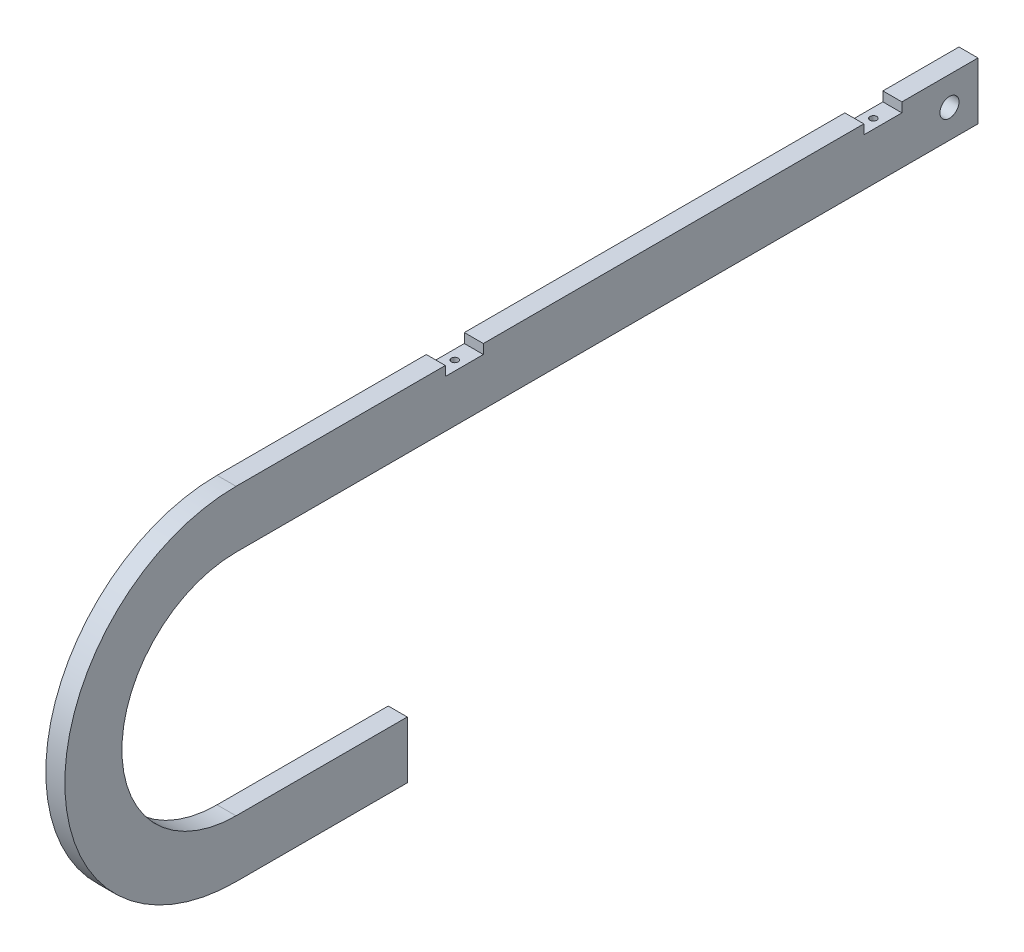
SolidWorks part; units mm, degrees
material "6061-T6 (SS)"
ref_plane "Front Plane" through (0, 0, 0) normal (0, 0, 1) x (1, 0, 0)
ref_plane "Top Plane" through (0, 0, 0) normal (0, 1, 0) x (1, 0, 0)
ref_plane "Right Plane" through (0, 0, 0) normal (1, 0, 0) x (0, 0, -1)
sketch "Sketch1" plane through (0, 0, 0) normal (1, 0, 0) x (0, 0, -1)
  line L0 (0, 38.1) -> (0, -38.1) construction
  line L1 (0, -38.1) -> (57.15, -38.1)
  line L2 (57.15, -38.1) -> (57.15, -57.15)
  line L3 (57.15, -57.15) -> (0, -57.15)
  line L4 (0, 57.15) -> (0, -57.15) construction
  line L5 (0, 38.1) -> (247.65, 38.1)
  line L6 (0, 57.15) -> (247.65, 57.15)
  line L7 (247.65, 57.15) -> (247.65, 38.1)
  line L8 (247.65, 47.625) -> (238.125, 47.625) construction
  line L9 (222.25, 57.15) -> (222.25, 53.975)
  line L10 (222.25, 53.975) -> (209.55, 53.975)
  line L11 (209.55, 53.975) -> (209.55, 57.15)
  line L12 (82.55, 57.15) -> (82.55, 53.975)
  line L13 (82.55, 53.975) -> (69.85, 53.975)
  line L14 (69.85, 53.975) -> (69.85, 57.15)
  arc A0 (0, -38.1) -> (0, 38.1) centre (0, 0) cw
  arc A1 (0, -57.15) -> (0, 57.15) centre (0, 0) cw
  circle A2 centre (238.125, 47.625) radius 3.175
  point P5 (0, 0)
  dimension "D1" = 38.1
  dimension "D2" = 57.15
  dimension "D3" = 9.525
  dimension "D4" = 6.35
  dimension "D5" = 3.175
  dimension "D6" = 12.7
  dimension "D7" = 25.4
  dimension "D8" = 127
  dimension "D9" = 57.15
  dimension "D10" = 190.5
extrude "Boss-Extrude1" add sketch "Sketch1" along normal mid plane 6.35 contours A1 L3 L2 L1 A0 L5 L7 L6 L9 L10 L11 L12 L13 L14 A2
sketch "Sketch2" plane through (0, 0, 0) normal (1, 0, 0) x (0, 0, -1)
  line L0 (25.4, 47.625) -> (203.2, 47.625) construction
  line L1 (-28.3981, 25.4) -> (22.4019, 25.4) construction
  line L2 (-28.3981, 25.4) -> (-28.3981, -25.4) construction
  line L3 (-28.3981, -25.4) -> (22.4019, -25.4) construction
  line L4 (22.4019, 25.4) -> (22.4019, -25.4) construction
  line L5 (-28.3981, 25.4) -> (22.4019, -25.4) construction
  line L6 (-28.3981, -25.4) -> (22.4019, 25.4) construction
  line L7 (-2.9981, 35.921) -> (32.923, 0) construction
  line L8 (-2.9981, 35.921) -> (-38.9191, 0) construction
  line L9 (-38.9191, 0) -> (-2.9981, -35.921) construction
  line L10 (32.923, 0) -> (-2.9981, -35.921) construction
  line L11 (-2.9981, 35.921) -> (-2.9981, -35.921) construction
  line L12 (-38.9191, 0) -> (32.923, 0) construction
  line L13 (203.2, 47.625) -> (47.4307, -38.1) construction
  line L14 (0, 38.1) -> (247.65, 38.1) construction
  line L15 (0, -38.1) -> (57.15, -38.1) construction
  circle A0 centre (-2.9981, 0) radius 25.4 construction
  arc A1 (0, 38.1) -> (0, -38.1) centre (0, 0) ccw construction
  arc A2 (0, 38.1) -> (0, -38.1) centre (0, 0) ccw construction
  arc A3 (47.4307, -38.1) -> (25.4, 47.625) centre (203.2, 47.625) cw construction
  point P0 (-2.9981, 0)
  dimension "D1" = 50.8
  dimension "D2" = 9.525
  dimension "D3" = 25.4
  dimension "D4" = 177.8
hole_wizard "#4-40 Tapped Hole1" positions "Sketch3" profile "Sketch4" tap size "#4-40" standard "ANSI Inch"
sketch "Sketch3" plane through (0, 53.975, 0) normal (0, 1, 0) x (1, 0, 0)
  line L0 (0, 203.2) -> (0, 47.4307) construction
  line L1 (3.175, 222.25) -> (-3.175, 222.25) construction
  line L2 (3.175, 69.85) -> (-3.175, 69.85) construction
  point P0 (0, 76.2)
  point P4 (0, 215.9)
  dimension "D1" = 6.35
  dimension "D2" = 6.35
sketch "Sketch4" plane through (0, 53.975, -76.2) normal (1, 0, 0) x (0, 0, 1)
  line L0 (0, 0) -> (0, 8.2992)
  line L1 (0, 8.2992) -> (1.1303, 7.62)
  line L2 (1.1303, 7.62) -> (1.1303, 0)
  line L5 (1.1303, 0) -> (0, 0)
  line L10 (0, 8.2992) -> (-1.1303, 7.62) construction
  line L11 (0, -6.35) -> (0, 107.95) construction
  dimension "Tap Drill Dia." = 2.2606
  dimension "Tap Drill Depth" = 7.62
  dimension "Drill Angle" = 118
cosmetic thread "Hole Thread1" parameters "D1"=5.588, "D2"=2.8448
cosmetic thread "Hole Thread2" parameters "D1"=5.588, "D2"=2.8448
equation "\"Thick\"= \"in\""
